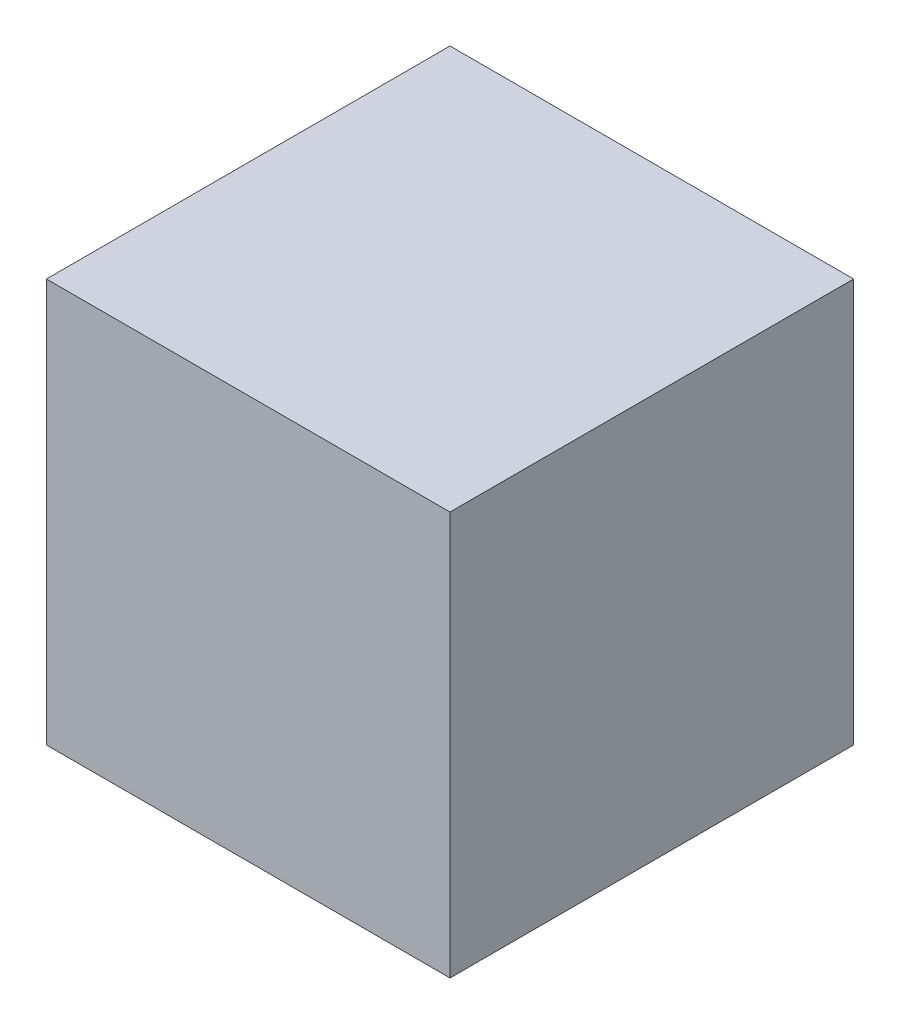
SolidWorks part; units mm, degrees
ref_plane "Front Plane" through (0, 0, 0) normal (0, 0, 1) x (1, 0, 0)
ref_plane "Top Plane" through (0, 0, 0) normal (0, 1, 0) x (1, 0, 0)
ref_plane "Right Plane" through (0, 0, 0) normal (1, 0, 0) x (0, 0, -1)
sketch "Sketch1" plane through (0, 0, 0) normal (0, 1, 0) x (1, 0, 0)
  line L1 (-12.7, 12.7) -> (12.7, 12.7)
  line L2 (-12.7, 12.7) -> (-12.7, -12.7)
  line L3 (-12.7, -12.7) -> (12.7, -12.7)
  line L4 (12.7, 12.7) -> (12.7, -12.7)
  line L5 (-12.7, 12.7) -> (12.7, -12.7) construction
  line L6 (-12.7, -12.7) -> (12.7, 12.7) construction
  point P0 (0, 0)
  dimension "D1" = 25.4
extrude "Boss-Extrude1" add sketch "Sketch1" along normal blind 25.4
